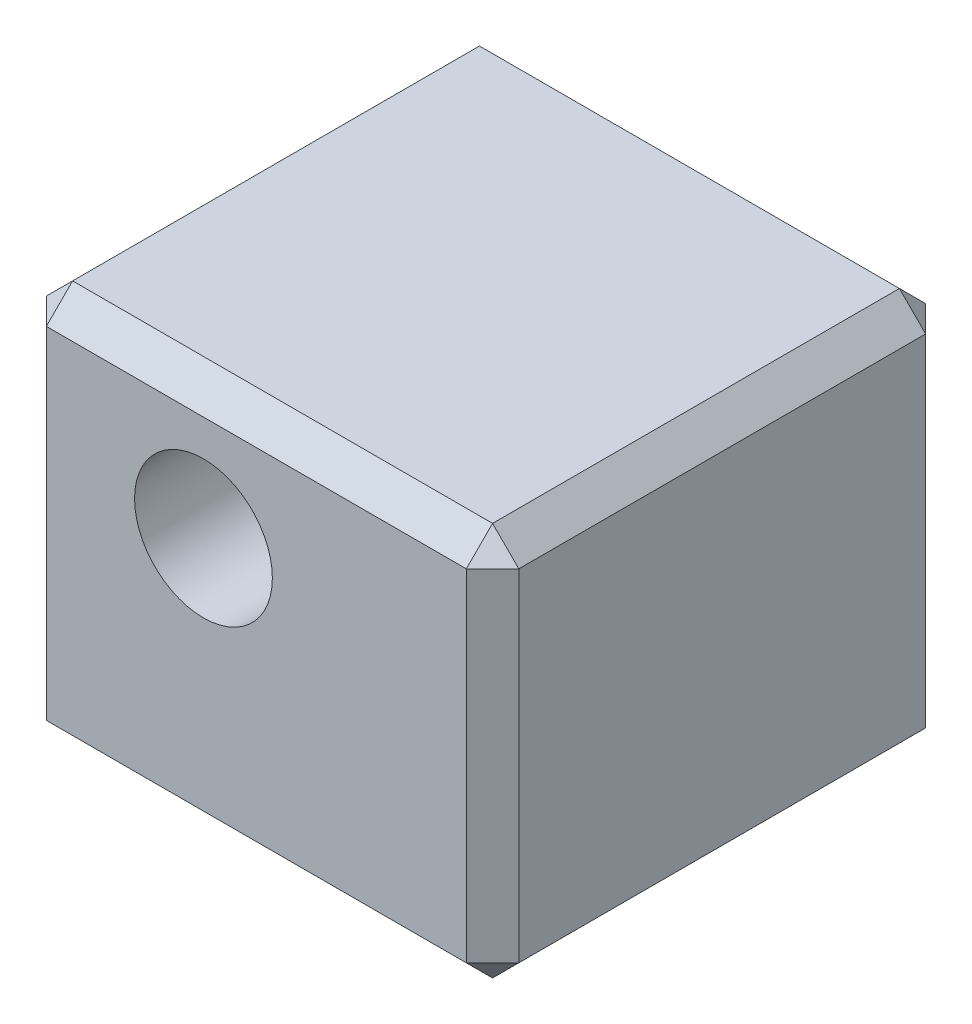
SolidWorks part; units mm, degrees
ref_plane "Front Plane" through (0, 0, 0) normal (0, 0, 1) x (1, 0, 0)
ref_plane "Top Plane" through (0, 0, 0) normal (0, 1, 0) x (1, 0, 0)
ref_plane "Right Plane" through (0, 0, 0) normal (1, 0, 0) x (0, 0, -1)
sketch "Sketch1" plane through (0, 0, 0) normal (0, 1, 0) x (1, 0, 0)
  line L0 (-13.2723, 2.6283) -> (4.7277, 2.6283)
  line L1 (4.7277, 2.6283) -> (4.7277, 20.6283)
  line L2 (4.7277, 20.6283) -> (-13.2723, 20.6283)
  line L3 (-13.2723, 20.6283) -> (-13.2723, 2.6283)
  dimension "D1" = 18
  dimension "D2" = 18
extrude "Boss-Extrude1" add sketch "Sketch1" along normal blind 15
sketch "Sketch2" plane through (0, 0, -2.6283) normal (0, 0, 1) x (1, 0, 0)
  line L0 (-13.2723, 7.5) -> (4.7277, 7.5) construction
  line L1 (-13.2723, 15) -> (-13.2723, 0) construction
  line L2 (4.7277, 15) -> (4.7277, 0) construction
  circle A0 centre (-6.2868, 10) radius 2.625
  dimension "D1" = 5.25
  dimension "D2" = 11.0145
  dimension "D3" = 10
extrude "Cut-Extrude1" cut sketch "Sketch2" against normal through all
sketch "Sketch3" plane through (0, 0, 0) normal (0, -1, 0) x (1, 0, 0)
  line L0 (-13.2723, -11.6283) -> (4.7277, -11.6283) construction
  line L1 (-13.2723, -20.6283) -> (-13.2723, -2.6283) construction
  line L2 (4.7277, -2.6283) -> (4.7277, -20.6283) construction
  line L3 (4.7277, -2.6283) -> (-13.2723, -20.6283) construction
  circle A1 centre (-4.2723, -11.6283) radius 5.75
  dimension "D1" = 11.5
  dimension "D3" = 18
extrude "Cut-Extrude2" cut sketch "Sketch3" against normal blind 7
sketch "Sketch5" plane through (0, 0, -2.6283) normal (0, 0, 1) x (1, 0, 0)
  line L0 (4.7277, 15) -> (4.7277, 0)
  line L1 (4.7277, 0) -> (-13.2723, 0)
  line L2 (-13.2723, 0) -> (-13.2723, 15)
  line L3 (-13.2723, 15) -> (4.7277, 15)
  line L4 (-13.2723, 15) -> (-13.2723, 0) construction
extrude "Cut-Extrude3" cut sketch "Sketch5" against normal blind 0.5
chamfer "Chamfer1" distance 1 angle 45 12 edges at (4.7277, 7.5, -20.6283) (4.7277, 15, -11.8783) (-4.2723, 15, -20.6283) (-13.2723, 7.5, -20.6283) (-13.2723, 15, -11.8783) (-13.2723, 7.5, -3.1283) (-4.2723, 15, -3.1283) (4.7277, 7.5, -3.1283) (4.7277, 0, -11.8783) (-4.2723, 0, -3.1283) (-13.2723, 0, -11.8783) (-4.2723, 0, -20.6283)
